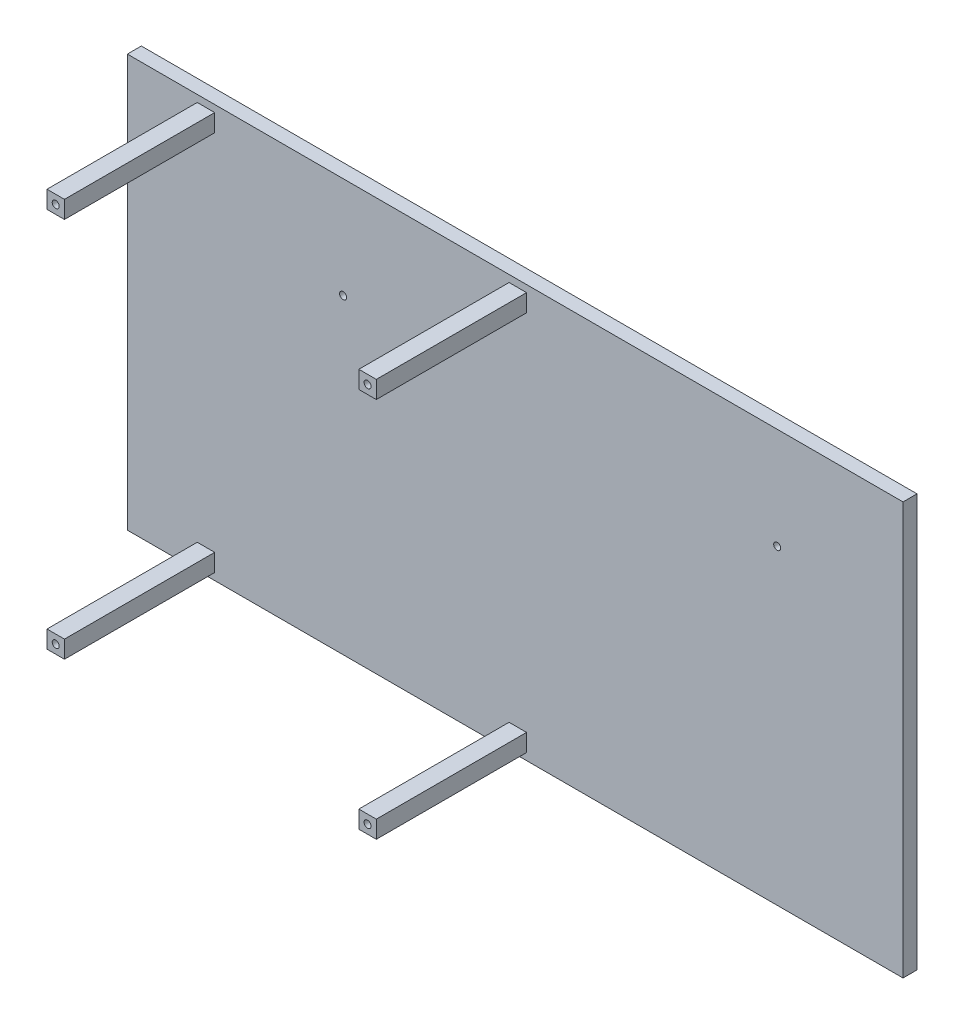
SolidWorks part; units mm, degrees
ref_plane "Alzado" through (0, 0, 0) normal (0, 0, 1) x (1, 0, 0)
ref_plane "Planta" through (0, 0, 0) normal (0, 1, 0) x (1, 0, 0)
ref_plane "Vista lateral" through (0, 0, 0) normal (1, 0, 0) x (0, 0, -1)
sketch "Sketch1" plane through (0, 0, 0) normal (0, 0, 1) x (1, 0, 0)
  line L1 (-99.7768, 38.058) -> (100.2232, 38.058)
  line L2 (-99.7768, 38.058) -> (-99.7768, -111.942)
  line L3 (-99.7768, -111.942) -> (100.2232, -111.942)
  line L4 (100.2232, 38.058) -> (100.2232, -111.942)
  dimension "D1" = 200
  dimension "D2" = 150
extrude "Boss-Extrude1" add sketch "Sketch1" along normal blind 4
sketch "Sketch2" plane through (100.2232, 0, 0) normal (1, 0, 0) x (0, 0, -1)
  line L1 (-4, 38.058) -> (0, 38.058)
  line L2 (-4, 38.058) -> (-4, -111.942)
  line L3 (-4, -111.942) -> (0, -111.942)
  line L4 (0, 38.058) -> (0, -111.942)
extrude "Boss-Extrude2" add sketch "Sketch2" along normal blind 50
sketch "Sketch3" plane through (0, 0, 0) normal (0, 0, -1) x (-1, 0, 0)
  line L0 (99.7768, 38.058) -> (99.7768, -111.942) construction
  line L1 (99.7768, -111.942) -> (-150.2232, -111.942) construction
  circle A0 centre (96.7768, -77.942) radius 1
  dimension "D1" = 3
  dimension "D2" = 34
extrude "Cut-Extrude1" cut sketch "Sketch3" against normal blind 21
sketch "Sketch4" plane through (0, 0, 0) normal (0, 0, -1) x (-1, 0, 0)
  line L0 (-150.2232, -111.942) -> (-150.2232, 38.058) construction
  circle A0 centre (-147.2232, -77.942) radius 1
  dimension "D1" = 3
extrude "Cut-Extrude2" cut sketch "Sketch4" against normal blind 21
sketch "Sketch5" plane through (0, 0, 0) normal (0, 0, -1) x (-1, 0, 0)
  circle A0 centre (-99.4232, -77.942) radius 1
  circle A1 centre (-147.2232, -77.942) radius 1 construction
  dimension "D1" = 47.8
extrude "Cut-Extrude3" cut sketch "Sketch5" against normal blind 21
sketch "Sketch6" plane through (0, 0, 4) normal (0, 0, 1) x (1, 0, 0)
  line L0 (150.2232, -111.942) -> (150.2232, -15.442) construction
  line L1 (150.2232, 38.058) -> (150.2232, -111.942) construction
  line L2 (150.2232, -15.442) -> (114.2032, -15.442) construction
  circle A0 centre (114.2032, -15.442) radius 1
  circle A1 centre (-10.0268, -15.442) radius 1
  dimension "D3" = 124.23
  dimension "D1" = 96.5
  dimension "D2" = 36.02
extrude "Cut-Extrude4" cut sketch "Sketch6" against normal through all
sketch "Sketch7" plane through (0, 0, 0) normal (0, 0, -1) x (-1, 0, 0)
  circle A0 centre (93.6327, -80.2492) radius 6.1441
extrude "Boss-Extrude3" add sketch "Sketch7" against normal blind 4
sketch "Sketch8" plane through (0, 0, 4) normal (0, 0, 1) x (1, 0, 0)
  line L0 (-10.0268, -15.442) -> (-10.0268, 11.558) construction
  line L1 (114.2032, -15.442) -> (113.837, 9.058) construction
  line L2 (-12.5268, 11.558) -> (-7.5268, 11.558)
  line L3 (-12.5268, 11.558) -> (-12.5268, 6.558)
  line L4 (-12.5268, 6.558) -> (-7.5268, 6.558)
  line L5 (-7.5268, 11.558) -> (-7.5268, 6.558)
  line L6 (-12.5268, 11.558) -> (-7.5268, 6.558) construction
  line L7 (-12.5268, 6.558) -> (-7.5268, 11.558) construction
  line L8 (116.337, 6.558) -> (111.337, 6.558)
  line L9 (116.337, 6.558) -> (116.337, 11.558)
  line L10 (116.337, 11.558) -> (111.337, 11.558)
  line L11 (111.337, 6.558) -> (111.337, 11.558)
  line L12 (116.337, 6.558) -> (111.337, 11.558) construction
  line L13 (116.337, 11.558) -> (111.337, 6.558) construction
  point P3 (-10.0268, 9.058)
  point P8 (113.837, 9.058)
  dimension "D1" = 27
  dimension "D2" = 5
  dimension "D3" = 5
  dimension "D4" = 2.5
  dimension "D5" = 5
extrude "Boss-Extrude4" add sketch "Sketch8" along normal blind 43
sketch "Sketch9" plane through (0, 0, 4) normal (0, 0, 1) x (1, 0, 0)
  line L1 (37.4732, 11.558) -> (42.4732, 11.558)
  line L2 (37.4732, 11.558) -> (37.4732, 6.558)
  line L3 (37.4732, 6.558) -> (42.4732, 6.558)
  line L4 (42.4732, 11.558) -> (42.4732, 6.558)
  line L5 (37.4732, 11.558) -> (42.4732, 6.558) construction
  line L6 (37.4732, 6.558) -> (42.4732, 11.558) construction
  point P0 (39.9732, 9.058)
  dimension "D1" = 5
  dimension "D2" = 45
extrude "Boss-Extrude5" add sketch "Sketch9" along normal blind 43
sketch "Sketch10" plane through (0, 0, 4) normal (0, 0, 1) x (1, 0, 0)
  line L1 (-67.5268, 11.558) -> (-62.5268, 11.558)
  line L2 (-67.5268, 11.558) -> (-67.5268, 6.558)
  line L3 (-67.5268, 6.558) -> (-62.5268, 6.558)
  line L4 (-62.5268, 11.558) -> (-62.5268, 6.558)
  line L5 (-67.5268, 11.558) -> (-62.5268, 6.558) construction
  line L6 (-67.5268, 6.558) -> (-62.5268, 11.558) construction
  point P0 (-65.0268, 9.058)
  dimension "D1" = 5
  dimension "D2" = 50
extrude "Boss-Extrude6" add sketch "Sketch10" along normal blind 43
sketch "Sketch11" plane through (0, 0, 4) normal (0, 0, 1) x (1, 0, 0)
  line L0 (-99.7768, -111.942) -> (150.2232, -111.942) construction
  line L1 (-99.7768, 38.058) -> (-69.7768, 38.058)
  line L2 (-99.7768, 38.058) -> (-99.7768, -111.942)
  line L3 (-99.7768, -111.942) -> (-69.7768, -111.942)
  line L4 (-69.7768, 38.058) -> (-69.7768, -111.942)
  line L5 (150.2232, 38.058) -> (150.2232, -111.942) construction
  dimension "D1" = 220
extrude "Cut-Extrude5" cut sketch "Sketch11" against normal blind 10
sketch "Sketch12" plane through (0, 0, 4) normal (0, 0, 1) x (1, 0, 0)
  line L0 (150.2232, 38.058) -> (150.2232, -111.942) construction
  line L1 (-69.7768, 38.058) -> (150.2232, 38.058)
  line L2 (-69.7768, 38.058) -> (-69.7768, 13.558)
  line L3 (-69.7768, 13.558) -> (150.2232, 13.558)
  line L4 (150.2232, 38.058) -> (150.2232, 13.558)
  line L5 (-7.5268, 11.558) -> (-12.5268, 11.558) construction
  dimension "D1" = 2
extrude "Cut-Extrude6" cut sketch "Sketch12" against normal blind 10
sketch "Sketch13" plane through (0, 0, 47) normal (0, 0, 1) x (1, 0, 0)
  line L0 (-69.7768, 13.558) -> (150.2232, 13.558) construction
  line L1 (141.9311, -10.2341) -> (101.0556, -10.2341)
  line L2 (141.9311, -10.2341) -> (141.9311, 13.558)
  line L3 (141.9311, 13.558) -> (101.0556, 13.558)
  line L4 (101.0556, -10.2341) -> (101.0556, 13.558)
  line L5 (141.9311, -10.2341) -> (101.0556, 13.558) construction
  line L6 (141.9311, 13.558) -> (101.0556, -10.2341) construction
  line L8 (9.9273, -16.0886) -> (-20.8496, -16.0886)
  line L9 (9.9273, -16.0886) -> (9.9273, 16.0886)
  line L10 (9.9273, 16.0886) -> (-20.8496, 16.0886)
  line L11 (-20.8496, -16.0886) -> (-20.8496, 16.0886)
  line L12 (9.9273, -16.0886) -> (-20.8496, 16.0886) construction
  line L13 (9.9273, 16.0886) -> (-20.8496, -16.0886) construction
  point P0 (121.4933, 1.662)
  point P7 (-5.4612, 0)
extrude "Cut-Extrude7" cut sketch "Sketch13" against normal up to vertex (43 mm away)
sketch "Sketch14" plane through (0, 0, 4) normal (0, 0, 1) x (1, 0, 0)
  line L0 (150.2232, 13.558) -> (150.2232, -111.942) construction
  line L1 (-69.7768, -111.942) -> (150.2232, -111.942)
  line L2 (-69.7768, -111.942) -> (-69.7768, -104.442)
  line L3 (-69.7768, -104.442) -> (150.2232, -104.442)
  line L4 (150.2232, -111.942) -> (150.2232, -104.442)
  dimension "D1" = 7.5
extrude "Cut-Extrude8" cut sketch "Sketch14" against normal blind 10
sketch "Sketch15" plane through (0, 0, 0) normal (0, 0, -1) x (-1, 0, 0)
  line L1 (69.7768, -104.442) -> (71.7768, -104.442)
  line L2 (69.7768, -104.442) -> (69.7768, 13.558)
  line L3 (69.7768, 13.558) -> (71.7768, 13.558)
  line L4 (71.7768, -104.442) -> (71.7768, 13.558)
  dimension "D1" = 2
extrude "Boss-Extrude7" add sketch "Sketch15" against normal blind 47
sketch "Sketch17" plane through (-71.7768, 0, 0) normal (-1, 0, 0) x (0, 0, 1)
  line L0 (0, -104.442) -> (0, -45.442) construction
  line L1 (0, -104.442) -> (0, 13.558) construction
  line L2 (0, -45.442) -> (10, -45.442) construction
  line L4 (6.5, -41.942) -> (13.5, -41.942)
  line L5 (6.5, -41.942) -> (6.5, -48.942)
  line L6 (6.5, -48.942) -> (13.5, -48.942)
  line L7 (13.5, -41.942) -> (13.5, -48.942)
  line L8 (6.5, -41.942) -> (13.5, -48.942) construction
  line L9 (6.5, -48.942) -> (13.5, -41.942) construction
  dimension "D1" = 59
  dimension "D2" = 10
  dimension "D3" = 7
  dimension "D4" = 7
extrude "Boss-Extrude8" add sketch "Sketch17" against normal blind 10
sketch "Sketch18" plane through (-71.7768, 0, 0) normal (-1, 0, 0) x (0, 0, 1)
  circle A0 centre (10, -45.442) radius 2.5
extrude "Cut-Extrude9" cut sketch "Sketch18" against normal blind 9
sketch "Sketch19" plane through (-62.7768, 0, 0) normal (-1, 0, 0) x (0, 0, 1)
  circle A0 centre (10, -45.442) radius 1
extrude "Boss-Extrude9" add sketch "Sketch19" along normal blind 9 separate body
fillet "Fillet1" radius 1 1 edges at (-71.7768, -45.442, 11)
sketch "Sketch20" plane through (-71.7768, 0, 0) normal (-1, 0, 0) x (0, 0, 1)
  line L1 (13.3193, -82.942) -> (6.1193, -82.942)
  line L2 (13.3193, -82.942) -> (13.3193, -97.442)
  line L3 (13.3193, -97.442) -> (6.1193, -97.442)
  line L4 (6.1193, -82.942) -> (6.1193, -97.442)
  dimension "D1" = 14.5
  dimension "D2" = 34
  dimension "D3" = 7.2
extrude "Boss-Extrude10" add sketch "Sketch20" against normal up to vertex (10 mm away)
sketch "Sketch21" plane through (-71.7768, 0, 0) normal (-1, 0, 0) x (0, 0, 1)
  line L1 (12.2701, -84.005) -> (7.3078, -84.005)
  line L2 (12.2701, -84.005) -> (12.2701, -96.3789)
  line L3 (12.2701, -96.3789) -> (7.3078, -96.3789)
  line L4 (7.3078, -84.005) -> (7.3078, -96.3789)
  line L5 (12.2701, -84.005) -> (7.3078, -96.3789) construction
  line L6 (12.2701, -96.3789) -> (7.3078, -84.005) construction
  point P0 (9.7889, -90.192)
extrude "Cut-Extrude10" cut sketch "Sketch21" against normal blind 9
sketch "Sketch22" plane through (-62.7768, 0, 0) normal (-1, 0, 0) x (0, 0, 1)
  line L0 (12.2701, -90.192) -> (7.3078, -90.192) construction
  line L1 (12.2701, -96.3789) -> (12.2701, -84.005) construction
  line L2 (7.3078, -84.005) -> (7.3078, -96.3789) construction
  line L3 (9.7889, -84.005) -> (9.7889, -90.192) construction
  line L4 (12.2701, -84.005) -> (7.3078, -84.005) construction
  line L6 (9.4002, -85.5769) -> (10.1776, -85.5769)
  line L7 (9.4002, -85.5769) -> (9.4002, -94.8071)
  line L8 (9.4002, -94.8071) -> (10.1776, -94.8071)
  line L9 (10.1776, -85.5769) -> (10.1776, -94.8071)
  line L10 (9.4002, -85.5769) -> (10.1776, -94.8071) construction
  line L11 (9.4002, -94.8071) -> (10.1776, -85.5769) construction
extrude "Boss-Extrude11" add sketch "Sketch22" along normal blind 8
sketch "Sketch23" plane through (-62.7768, 0, 0) normal (-1, 0, 0) x (0, 0, 1)
  line L0 (10.1776, -94.8071) -> (10.1776, -85.5769) construction
  line L1 (10.1776, -85.9244) -> (10.7685, -85.9244)
  line L2 (10.1776, -85.9244) -> (10.1776, -86.7244)
  line L3 (10.1776, -86.7244) -> (10.7685, -86.7244)
  line L4 (10.7685, -85.9244) -> (10.7685, -86.7244)
  line L5 (10.1776, -94.8071) -> (10.1776, -85.5769) construction
  line L6 (10.1776, -88.8258) -> (10.7685, -88.8258)
  line L7 (10.1776, -88.8258) -> (10.1776, -87.9896)
  line L8 (10.1776, -87.9896) -> (10.7685, -87.9896)
  line L9 (10.7685, -88.8258) -> (10.7685, -87.9896)
  line L11 (10.1776, -91.0887) -> (10.7685, -91.0887)
  line L12 (10.1776, -91.0887) -> (10.1776, -91.8758)
  line L13 (10.1776, -91.8758) -> (10.7685, -91.8758)
  line L14 (10.7685, -91.0887) -> (10.7685, -91.8758)
  line L15 (10.1776, -93.3024) -> (10.7685, -93.3024)
  line L16 (10.1776, -93.3024) -> (10.1776, -94.1387)
  line L17 (10.1776, -94.1387) -> (10.7685, -94.1387)
  line L18 (10.7685, -93.3024) -> (10.7685, -94.1387)
  dimension "D1" = 0.8
extrude "Boss-Extrude12" add sketch "Sketch23" along normal blind 7
sketch "Sketch24" plane through (0, 0, 4) normal (0, 0, 1) x (1, 0, 0)
  line L0 (42.4732, 6.558) -> (42.4732, -37.442) construction
  line L2 (42.4732, -37.442) -> (37.4732, -37.442)
  line L3 (42.4732, -37.442) -> (42.4732, -42.442)
  line L4 (42.4732, -42.442) -> (37.4732, -42.442)
  line L5 (37.4732, -37.442) -> (37.4732, -42.442)
  dimension "D1" = 44
  dimension "D2" = 5
extrude "Boss-Extrude13" add sketch "Sketch24" along normal up to vertex (43 mm away)
sketch "Sketch25" plane through (0, 0, 4) normal (0, 0, 1) x (1, 0, 0)
  line L0 (42.4732, 6.558) -> (42.4732, -63.442) construction
  line L1 (37.4732, -68.442) -> (-67.5268, -68.442) construction
  line L2 (42.4732, -63.442) -> (37.4732, -63.442)
  line L3 (42.4732, -63.442) -> (42.4732, -68.442)
  line L4 (42.4732, -68.442) -> (37.4732, -68.442)
  line L5 (37.4732, -63.442) -> (37.4732, -68.442)
  line L7 (-67.5268, -68.442) -> (-62.5268, -68.442)
  line L8 (-67.5268, -68.442) -> (-67.5268, -63.442)
  line L9 (-67.5268, -63.442) -> (-62.5268, -63.442)
  line L10 (-62.5268, -68.442) -> (-62.5268, -63.442)
  dimension "D1" = 70
  dimension "D2" = 5
  dimension "D3" = 5
  dimension "D4" = 5
extrude "Boss-Extrude14" add sketch "Sketch25" along normal up to vertex (43 mm away)
sketch "Sketch26" plane through (0, 0, 47) normal (0, 0, 1) x (1, 0, 0)
  line L1 (42.4732, -42.442) -> (37.4732, -42.442)
  line L2 (42.4732, -42.442) -> (42.4732, -37.442)
  line L3 (42.4732, -37.442) -> (37.4732, -37.442)
  line L4 (37.4732, -42.442) -> (37.4732, -37.442)
extrude "Cut-Extrude11" cut sketch "Sketch26" against normal up to vertex
sketch "Sketch27" plane through (0, 0, 4) normal (0, 0, 1) x (1, 0, 0)
  line L0 (150.2232, -104.442) -> (-69.7768, -104.442) construction
  line L1 (42.4732, -102.442) -> (37.4732, -102.442)
  line L2 (42.4732, -102.442) -> (42.4732, -97.442)
  line L3 (42.4732, -97.442) -> (37.4732, -97.442)
  line L4 (37.4732, -102.442) -> (37.4732, -97.442)
  line L5 (42.4732, 6.558) -> (42.4732, -104.442) construction
  dimension "D1" = 5
  dimension "D2" = 5
  dimension "D3" = 2
  dimension "D4" = 5
extrude "Boss-Extrude15" add sketch "Sketch27" along normal up to vertex (43 mm away)
sketch "Sketch28" plane through (0, 0, 47) normal (0, 0, 1) x (1, 0, 0)
  line L1 (37.4732, -63.442) -> (42.4732, -63.442)
  line L2 (37.4732, -63.442) -> (37.4732, -68.442)
  line L3 (37.4732, -68.442) -> (42.4732, -68.442)
  line L4 (42.4732, -63.442) -> (42.4732, -68.442)
extrude "Cut-Extrude12" cut sketch "Sketch28" against normal up to vertex
sketch "Sketch29" plane through (0, 0, 47) normal (0, 0, 1) x (1, 0, 0)
  line L0 (-71.7768, -104.442) -> (-71.7768, 13.558) construction
  line L1 (-69.7768, -104.442) -> (-71.7768, -104.442)
  line L2 (-69.7768, -104.442) -> (-69.7768, -38.032)
  line L3 (-69.7768, -38.032) -> (-71.7768, -38.032)
  line L4 (-71.7768, -104.442) -> (-71.7768, -38.032)
extrude "Boss-Extrude16" add sketch "Sketch29" against normal up to vertex (47 mm away)
sketch "Sketch30" plane through (0, 0, 13.5) normal (0, 0, 1) x (1, 0, 0)
  line L0 (-69.7768, -104.442) -> (-69.7768, 13.558) construction
  line L1 (-61.7768, -41.942) -> (-69.7768, -41.942)
  line L2 (-61.7768, -41.942) -> (-61.7768, -48.942)
  line L3 (-61.7768, -48.942) -> (-69.7768, -48.942)
  line L4 (-69.7768, -41.942) -> (-69.7768, -48.942)
  line L5 (-61.7768, -82.942) -> (-69.7768, -82.942)
  line L6 (-61.7768, -82.942) -> (-61.7768, -97.442)
  line L7 (-61.7768, -97.442) -> (-69.7768, -97.442)
  line L8 (-69.7768, -82.942) -> (-69.7768, -97.442)
  line L9 (-61.7768, -97.442) -> (-69.7768, -97.442) construction
extrude "Cut-Extrude13" cut sketch "Sketch30" against normal up to vertex (9.5 mm away)
sketch "Sketch31" plane through (0, 0, 47) normal (0, 0, 1) x (1, 0, 0)
  line L1 (-62.5268, -63.442) -> (-67.5268, -63.442)
  line L2 (-62.5268, -63.442) -> (-62.5268, -68.442)
  line L3 (-62.5268, -68.442) -> (-67.5268, -68.442)
  line L4 (-67.5268, -63.442) -> (-67.5268, -68.442)
extrude "Cut-Extrude14" cut sketch "Sketch31" against normal up to vertex (43 mm away)
sketch "Sketch32" plane through (0, 0, 4) normal (0, 0, 1) x (1, 0, 0)
  line L0 (-67.5268, 6.558) -> (-67.5268, -102.442) construction
  line L1 (150.2232, -104.442) -> (-69.7768, -104.442) construction
  line L2 (-67.5268, -102.442) -> (-62.5268, -102.442)
  line L3 (-67.5268, -102.442) -> (-67.5268, -97.442)
  line L4 (-67.5268, -97.442) -> (-62.5268, -97.442)
  line L5 (-62.5268, -102.442) -> (-62.5268, -97.442)
  dimension "D1" = 5
  dimension "D2" = 5
  dimension "D3" = 2
extrude "Boss-Extrude17" add sketch "Sketch32" along normal up to vertex (43 mm away)
sketch "Sketch35" plane through (0, 0, 4) normal (0, 0, 1) x (1, 0, 0)
  line L0 (42.4732, 6.558) -> (42.4732, -37.442) construction
  line L3 (-10.0268, -37.442) -> (-15.0268, -37.442)
  line L4 (-10.0268, -37.442) -> (-10.0268, -42.442)
  line L5 (-10.0268, -42.442) -> (-15.0268, -42.442)
  line L6 (-15.0268, -37.442) -> (-15.0268, -42.442)
  dimension "D1" = 44
  dimension "D2" = 52.5
  dimension "D3" = 5
  dimension "D4" = 5
extrude "Boss-Extrude18" add sketch "Sketch35" along normal up to vertex (43 mm away)
sketch "Sketch37" plane through (0, 0, 47) normal (0, 0, 1) x (1, 0, 0)
  circle A0 centre (39.9732, 9.058) radius 1
  circle A1 centre (39.9732, -99.942) radius 1
  circle A2 centre (-65.0268, -99.942) radius 1
  circle A3 centre (-65.0268, 9.058) radius 1
  circle A4 centre (-12.5268, -39.942) radius 1
extrude "Cut-Extrude16" cut sketch "Sketch37" against normal blind 3
sketch "Sketch38" plane through (0, 0, 47) normal (0, 0, 1) x (1, 0, 0)
  line L1 (-71.7768, 13.558) -> (-69.7768, 13.558)
  line L2 (-71.7768, 13.558) -> (-71.7768, -104.442)
  line L3 (-71.7768, -104.442) -> (-69.7768, -104.442)
  line L4 (-69.7768, 13.558) -> (-69.7768, -104.442)
extrude "Cut-Extrude17" cut sketch "Sketch38" against normal up to vertex
sketch "Sketch39" plane through (0, 0, 4) normal (0, 0, 1) x (1, 0, 0)
  line L0 (-71.7768, 13.558) -> (150.2232, 13.558) construction
  line L1 (-46.7768, 11.558) -> (-51.7768, 11.558)
  line L2 (-46.7768, 11.558) -> (-46.7768, 6.558)
  line L3 (-46.7768, 6.558) -> (-51.7768, 6.558)
  line L4 (-51.7768, 11.558) -> (-51.7768, 6.558)
  line L5 (-46.7768, 11.558) -> (-51.7768, 6.558) construction
  line L6 (-46.7768, 6.558) -> (-51.7768, 11.558) construction
  line L7 (-71.7768, 13.558) -> (-71.7768, -104.442) construction
  line L8 (150.2232, -104.442) -> (-71.7768, -104.442) construction
  line L9 (-51.7768, -97.442) -> (-46.7768, -97.442)
  line L10 (-51.7768, -97.442) -> (-51.7768, -102.442)
  line L11 (-51.7768, -102.442) -> (-46.7768, -102.442)
  line L12 (-46.7768, -97.442) -> (-46.7768, -102.442)
  point P0 (-49.2768, 9.058)
  dimension "D1" = 5
  dimension "D2" = 5
  dimension "D3" = 2
  dimension "D4" = 20
  dimension "D5" = 5
  dimension "D6" = 5
  dimension "D7" = 2
extrude "Boss-Extrude19" add sketch "Sketch39" along normal up to vertex (43 mm away)
sketch "Sketch40" plane through (0, 0, 47) normal (0, 0, 1) x (1, 0, 0)
  line L0 (-62.5268, 6.558) -> (-62.5268, 11.558) construction
  line L1 (-67.5268, 11.558) -> (-62.5268, 11.558)
  line L2 (-67.5268, 11.558) -> (-67.5268, 6.558)
  line L3 (-67.5268, 6.558) -> (-62.5268, 6.558)
  line L4 (-62.5268, 11.558) -> (-62.5268, 6.558)
  line L5 (-62.5268, 6.558) -> (-62.5268, 11.558) construction
  line L7 (-62.5268, -102.442) -> (-67.5268, -102.442)
  line L8 (-62.5268, -102.442) -> (-62.5268, -97.442)
  line L9 (-62.5268, -97.442) -> (-67.5268, -97.442)
  line L10 (-67.5268, -102.442) -> (-67.5268, -97.442)
extrude "Cut-Extrude18" cut sketch "Sketch40" against normal up to vertex
sketch "Sketch41" plane through (0, 0, 47) normal (0, 0, 1) x (1, 0, 0)
  circle A0 centre (-49.2768, 9.058) radius 1
  circle A1 centre (-49.2768, -99.942) radius 1
extrude "Cut-Extrude19" cut sketch "Sketch41" against normal up to surface (3 mm away) up to face at (-11.5268, -39.942, 44)
sketch "Sketch42" plane through (0, 0, 47) normal (0, 0, 1) x (1, 0, 0)
  line L1 (-21.9195, -29.7923) -> (0, -29.7923)
  line L2 (-21.9195, -29.7923) -> (-21.9195, -55.9964)
  line L3 (-21.9195, -55.9964) -> (0, -55.9964)
  line L4 (0, -29.7923) -> (0, -55.9964)
extrude "Cut-Extrude20" cut sketch "Sketch42" against normal up to vertex
sketch "Sketch43" plane through (0, 0, 4) normal (0, 0, 1) x (1, 0, 0)
  line L0 (150.2232, 13.558) -> (150.2232, -104.442) construction
  line L1 (150.2232, -95.5451) -> (91.146, -95.5451)
  line L2 (150.2232, -95.5451) -> (150.2232, -59.6358)
  line L3 (150.2232, -59.6358) -> (91.146, -59.6358)
  line L4 (91.146, -95.5451) -> (91.146, -59.6358)
extrude "Boss-Extrude20" add sketch "Sketch43" against normal up to vertex (4 mm away)
